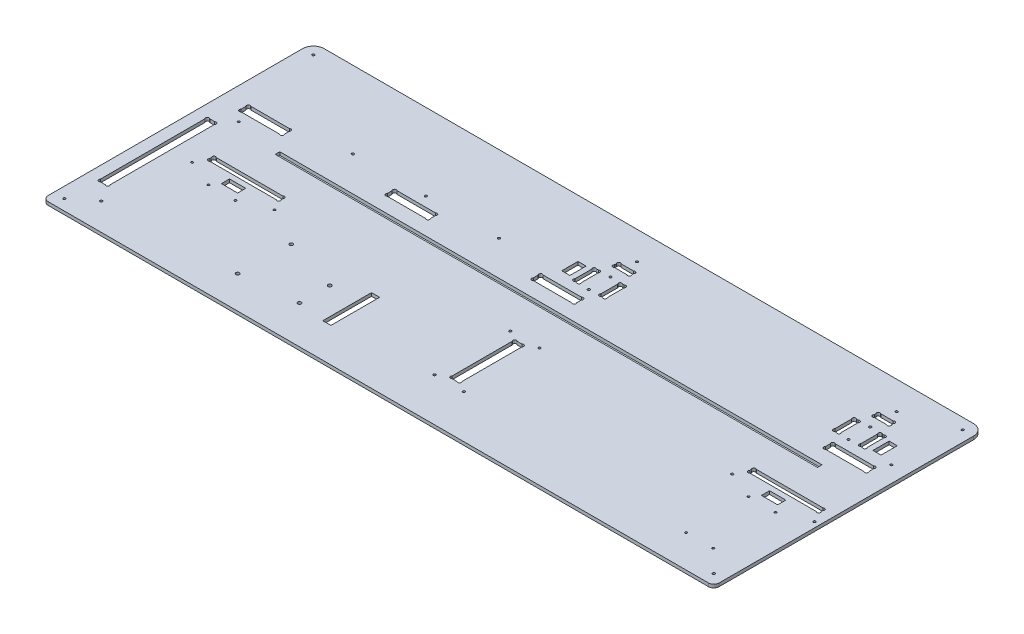
SolidWorks part; units mm, degrees
ref_plane "Plan de face" through (0, 0, 0) normal (0, 0, 1) x (1, 0, 0)
ref_plane "Plan de dessus" through (0, 0, 0) normal (0, 1, 0) x (1, 0, 0)
ref_plane "Plan de droite" through (0, 0, 0) normal (1, 0, 0) x (0, 0, -1)
sketch "Esquisse1" plane through (0, 0, 0) normal (0, 1, 0) x (1, 0, 0)
  line L26 (317, 211.2627) -> (317, 212.7373)
  line L28 (319.2627, 215) -> (330.7373, 215)
  line L29 (333, 211.2627) -> (333, 212.7373)
  line L30 (330.7373, 209) -> (319.2627, 209)
  line L31 (312.2627, 179.5) -> (313.7373, 179.5)
  line L32 (312.2627, 199.5) -> (313.7373, 199.5)
  line L33 (310, 197.2373) -> (310, 181.7627)
  line L34 (316, 181.7627) -> (316, 197.2373)
  line L35 (334, 181.7627) -> (334, 197.2373)
  line L36 (340, 197.2373) -> (340, 181.7627)
  line L37 (337.7373, 199.5) -> (336.2627, 199.5)
  line L38 (337.7373, 179.5) -> (336.2627, 179.5)
  line L39 (552.2627, 179.5) -> (553.7373, 179.5)
  line L40 (552.2627, 199.5) -> (553.7373, 199.5)
  line L41 (550, 197.2373) -> (550, 181.7627)
  line L42 (556, 181.7627) -> (556, 197.2373)
  line L43 (574, 181.7627) -> (574, 197.2373)
  line L44 (580, 197.2373) -> (580, 181.7627)
  line L45 (577.7373, 199.5) -> (576.2627, 199.5)
  line L46 (577.7373, 179.5) -> (576.2627, 179.5)
  line L47 (559.2627, 209) -> (570.7373, 209)
  line L48 (557, 211.2627) -> (557, 212.7373)
  line L49 (570.7373, 215) -> (559.2627, 215)
  line L50 (573, 211.2627) -> (573, 212.7373)
  line L55 (560, 167.7373) -> (560, 163.2627)
  line L56 (600, 167.7373) -> (600, 163.2627)
  line L57 (562.2627, 170) -> (597.7373, 170)
  line L58 (597.7373, 161) -> (562.2627, 161)
  line L59 (292.2627, 161) -> (327.7373, 161)
  line L60 (327.7373, 170) -> (292.2627, 170)
  line L61 (290, 167.7373) -> (290, 163.2627)
  line L62 (330, 167.7373) -> (330, 163.2627)
  line L64 (20, 167.7373) -> (20, 163.2627)
  line L65 (60, 167.7373) -> (60, 163.2627)
  line L66 (22.2627, 170) -> (57.7373, 170)
  line L67 (57.7373, 161) -> (22.2627, 161)
  line L70 (155, 167.7373) -> (155, 163.2627)
  line L71 (195, 167.7373) -> (195, 163.2627)
  line L72 (157.2627, 170) -> (192.7373, 170)
  line L73 (192.7373, 161) -> (157.2627, 161)
  line L76 (10, 250) -> (610, 250)
  line L77 (0, 240) -> (0, 0)
  line L78 (0, 0) -> (620, 0)
  line L79 (620, 240) -> (620, 0)
  line L84 (13.2627, 40) -> (17.7373, 40)
  line L85 (13.2627, 141) -> (17.7373, 141)
  line L86 (11, 138.7373) -> (11, 42.2627)
  line L87 (20, 42.2627) -> (20, 138.7373)
  line L98 (337.7373, 45) -> (333.2627, 45)
  line L99 (337.7373, 105) -> (333.2627, 105)
  line L100 (340, 47.2627) -> (340, 102.7373)
  line L101 (331, 102.7373) -> (331, 47.2627)
  line L109 (610, 109.2627) -> (610, 110.7373)
  line L110 (544, 109.2627) -> (544, 110.7373)
  line L111 (607.7373, 107) -> (546.2627, 107)
  line L112 (546.2627, 113) -> (607.7373, 113)
  line L113 (108.7373, 113) -> (47.2627, 113)
  line L114 (47.2627, 107) -> (108.7373, 107)
  line L115 (111, 109.2627) -> (111, 110.7373)
  line L116 (45, 109.2627) -> (45, 110.7373)
  arc A0 (319.2627, 215) -> (317, 212.7373) centre (318.1314, 213.8686) ccw
  arc A1 (319.2627, 209) -> (317, 211.2627) centre (318.1314, 210.1314) cw
  arc A2 (330.7373, 209) -> (333, 211.2627) centre (331.8686, 210.1314) ccw
  arc A3 (330.7373, 215) -> (333, 212.7373) centre (331.8686, 213.8686) cw
  arc A4 (313.7373, 179.5) -> (316, 181.7627) centre (314.8686, 180.6314) ccw
  arc A5 (312.2627, 179.5) -> (310, 181.7627) centre (311.1314, 180.6314) cw
  arc A6 (312.2627, 199.5) -> (310, 197.2373) centre (311.1314, 198.3686) ccw
  arc A7 (313.7373, 199.5) -> (316, 197.2373) centre (314.8686, 198.3686) cw
  arc A8 (336.2627, 179.5) -> (334, 181.7627) centre (335.1314, 180.6314) cw
  arc A9 (336.2627, 199.5) -> (334, 197.2373) centre (335.1314, 198.3686) ccw
  arc A10 (337.7373, 199.5) -> (340, 197.2373) centre (338.8686, 198.3686) cw
  arc A11 (337.7373, 179.5) -> (340, 181.7627) centre (338.8686, 180.6314) ccw
  arc A12 (552.2627, 179.5) -> (550, 181.7627) centre (551.1314, 180.6314) cw
  arc A13 (552.2627, 199.5) -> (550, 197.2373) centre (551.1314, 198.3686) ccw
  arc A14 (553.7373, 199.5) -> (556, 197.2373) centre (554.8686, 198.3686) cw
  arc A15 (553.7373, 179.5) -> (556, 181.7627) centre (554.8686, 180.6314) ccw
  arc A16 (576.2627, 199.5) -> (574, 197.2373) centre (575.1314, 198.3686) ccw
  arc A17 (577.7373, 199.5) -> (580, 197.2373) centre (578.8686, 198.3686) cw
  arc A18 (577.7373, 179.5) -> (580, 181.7627) centre (578.8686, 180.6314) ccw
  arc A19 (576.2627, 179.5) -> (574, 181.7627) centre (575.1314, 180.6314) cw
  arc A20 (559.2627, 215) -> (557, 212.7373) centre (558.1314, 213.8686) ccw
  arc A21 (559.2627, 209) -> (557, 211.2627) centre (558.1314, 210.1314) cw
  arc A22 (570.7373, 209) -> (573, 211.2627) centre (571.8686, 210.1314) ccw
  arc A23 (570.7373, 215) -> (573, 212.7373) centre (571.8686, 213.8686) cw
  arc A29 (560, 163.2627) -> (562.2627, 161) centre (561.1314, 162.1314) ccw
  arc A30 (560, 167.7373) -> (562.2627, 170) centre (561.1314, 168.8686) cw
  arc A31 (600, 167.7373) -> (597.7373, 170) centre (598.8686, 168.8686) ccw
  arc A32 (600, 163.2627) -> (597.7373, 161) centre (598.8686, 162.1314) cw
  arc A34 (290, 163.2627) -> (292.2627, 161) centre (291.1314, 162.1314) ccw
  arc A35 (290, 167.7373) -> (292.2627, 170) centre (291.1314, 168.8686) cw
  arc A36 (330, 167.7373) -> (327.7373, 170) centre (328.8686, 168.8686) ccw
  arc A37 (330, 163.2627) -> (327.7373, 161) centre (328.8686, 162.1314) cw
  arc A40 (20, 163.2627) -> (22.2627, 161) centre (21.1314, 162.1314) ccw
  arc A41 (20, 167.7373) -> (22.2627, 170) centre (21.1314, 168.8686) cw
  arc A42 (60, 167.7373) -> (57.7373, 170) centre (58.8686, 168.8686) ccw
  arc A43 (60, 163.2627) -> (57.7373, 161) centre (58.8686, 162.1314) cw
  arc A44 (155, 163.2627) -> (157.2627, 161) centre (156.1314, 162.1314) ccw
  arc A45 (155, 167.7373) -> (157.2627, 170) centre (156.1314, 168.8686) cw
  arc A46 (195, 163.2627) -> (192.7373, 161) centre (193.8686, 162.1314) cw
  arc A47 (195, 167.7373) -> (192.7373, 170) centre (193.8686, 168.8686) ccw
  arc A50 (17.7373, 40) -> (20, 42.2627) centre (18.8686, 41.1314) ccw
  arc A52 (13.2627, 40) -> (11, 42.2627) centre (12.1314, 41.1314) cw
  arc A53 (17.7373, 141) -> (20, 138.7373) centre (18.8686, 139.8686) cw
  arc A54 (13.2627, 141) -> (11, 138.7373) centre (12.1314, 139.8686) ccw
  arc A56 (10, 250) -> (0, 240) centre (10, 240) ccw
  arc A57 (610, 250) -> (620, 240) centre (610, 240) cw
  arc A59 (331, 47.2627) -> (333.2627, 45) centre (332.1314, 46.1314) ccw
  arc A60 (340, 47.2627) -> (337.7373, 45) centre (338.8686, 46.1314) cw
  arc A61 (331, 102.7373) -> (333.2627, 105) centre (332.1314, 103.8686) cw
  arc A62 (340, 102.7373) -> (337.7373, 105) centre (338.8686, 103.8686) ccw
  arc A64 (607.7373, 107) -> (610, 109.2627) centre (608.8686, 108.1314) ccw
  circle A65 centre (539, 98) radius 1.1
  arc A66 (607.7373, 113) -> (610, 110.7373) centre (608.8686, 111.8686) cw
  circle A67 centre (615, 98) radius 1.1
  arc A68 (546.2627, 113) -> (544, 110.7373) centre (545.1314, 111.8686) ccw
  arc A69 (546.2627, 107) -> (544, 109.2627) centre (545.1314, 108.1314) cw
  arc A70 (108.7373, 107) -> (111, 109.2627) centre (109.8686, 108.1314) ccw
  arc A71 (108.7373, 113) -> (111, 110.7373) centre (109.8686, 111.8686) cw
  arc A73 (47.2627, 113) -> (45, 110.7373) centre (46.1314, 111.8686) ccw
  arc A75 (47.2627, 107) -> (45, 109.2627) centre (46.1314, 108.1314) cw
  point P1 (337, 199.5)
  point P7 (340, 189.5)
  dimension "D25" = 6
  dimension "D28" = 16
  dimension "D29" = 20
  dimension "D32" = 9.5
  dimension "D33" = 35
  dimension "D39" = 10
  dimension "D49" = 1.1314
  dimension "D57" = 6
  dimension "D55" = 10
  dimension "D62" = 5
  dimension "D63" = 1.6
  dimension "D64" = 9
  dimension "D65" = 1.1314
  dimension "D66" = 1.1314
  dimension "D67" = 620
  dimension "D9" = 2.2627
  dimension "D10" = 1.6
  dimension "D78" = 3.7373
  dimension "D14" = 1.6
  dimension "D36" = 1.6
  dimension "D61" = 1.6
  dimension "D95" = 1.6
  dimension "D107" = 1.6
  dimension "D118" = 1.6
  dimension "D119" = 1.6
  dimension "D128" = 6
  dimension "D141" = 1.6
  dimension "D58" = 2.2
  dimension "D2" = 250
  dimension "D8" = 20
  dimension "D13" = 40
  dimension "D16" = 1.1314
  dimension "D17" = 1.1314
  dimension "D19" = 2.2627
  dimension "D20" = 2.2627
  dimension "D21" = 80
  dimension "D22" = 9
  dimension "D23" = 1.1314
  dimension "D24" = 1.1314
  dimension "D26" = 6
  dimension "D27" = 6
  dimension "D30" = 40
  dimension "D31" = 18
  dimension "D37" = 1.1314
  dimension "D38" = 2.2627
  dimension "D40" = 1.1314
  dimension "D41" = 1.1314
  dimension "D42" = 1.1314
  dimension "D43" = 1.1314
  dimension "D45" = 1
  dimension "D46" = 1.1314
  dimension "D47" = 1.1314
  dimension "D48" = 1.1314
  dimension "D51" = 3.7373
  dimension "D52" = 66
  dimension "D53" = 10
  dimension "D54" = 66
  dimension "D56" = 107
  dimension "D59" = 1.1314
  dimension "D60" = 2.2627
  dimension "D68" = 60
  dimension "D70" = 6
  dimension "D72" = 1.1314
  dimension "D73" = 1.1314
  dimension "D74" = 63.7373
  dimension "D75" = 2.2627
  dimension "D76" = 2.2627
  dimension "D77" = 45
  dimension "D79" = 45
  dimension "D83" = 280
  dimension "D84" = 1.1314
  dimension "D85" = 1.1314
  dimension "D86" = 1.1314
  dimension "D87" = 1.1314
  dimension "D88" = 9
  dimension "D89" = 101
  dimension "D90" = 40
  dimension "D91" = 11
  dimension "D96" = 1.1314
  dimension "D97" = 1.1314
  dimension "D98" = 1.1314
  dimension "D100" = 1.1314
  dimension "D105" = 9
  dimension "D106" = 40
  dimension "D108" = 20
  dimension "D109" = 80
  dimension "D110" = 1.1314
  dimension "D111" = 1.1314
  dimension "D112" = 1.1314
  dimension "D113" = 1.1314
  dimension "D114" = 40
  dimension "D115" = 95
  dimension "D116" = 95
  dimension "D117" = 40
  dimension "D120" = 1.1314
  dimension "D121" = 1.1314
  dimension "D122" = 1.1314
  dimension "D123" = 1.1314
  dimension "D124" = 1.1314
  dimension "D125" = 1.1314
  dimension "D126" = 1.1314
  dimension "D127" = 1.1314
  dimension "D129" = 6
  dimension "D130" = 6
  dimension "D132" = 20
  dimension "D133" = 16
  dimension "D135" = 35
  dimension "D136" = 9.5
  dimension "D139" = 1
  dimension "D140" = 18
  dimension "D142" = 1.1314
  dimension "D143" = 1.1314
  dimension "D144" = 1.1314
  dimension "D145" = 1.1314
  dimension "D146" = 1.1314
  dimension "D147" = 1.1314
  dimension "D148" = 1.1314
  dimension "D149" = 1.1314
  dimension "D150" = 1.1314
  dimension "D151" = 1.1314
  dimension "D152" = 1.1314
  dimension "D153" = 1.1314
  dimension "D154" = 9
  dimension "D155" = 5
extrude "Extrusion1" add sketch "Esquisse1" along normal blind 3
sketch "Esquisse2" plane through (0, 3, 0) normal (0, 1, 0) x (-1, 0, 0)
  line L0 (-610, -250) -> (-10, -250) construction
  line L5 (-620, 21.4973) -> (-620, -261.3021) construction
  line L7 (-573, -142.8) -> (-72, -142.8)
  line L8 (-573, -142.8) -> (-573, -147)
  line L9 (-573, -147) -> (-72, -147)
  line L10 (-72, -142.8) -> (-72, -147)
  dimension "D1" = 47
  dimension "D2" = 4.2
  dimension "D3" = 501
  dimension "D4" = 103
extrude "Enlèv. mat.-Extru.1" cut sketch "Esquisse2" against normal through all
sketch "Esquisse3" plane through (0, 3, 0) normal (0, 1, 0) x (1, 0, 0)
  line L0 (574, 197.2373) -> (574, 181.7627) construction
  line L1 (556, 181.7627) -> (556, 197.2373) construction
  line L2 (559.2627, 209) -> (570.7373, 209) construction
  line L4 (576.2627, 179.5) -> (577.7373, 179.5) construction
  line L5 (577.7373, 199.5) -> (576.2627, 199.5) construction
  line L6 (334, 197.2373) -> (334, 181.7627) construction
  circle A0 centre (565, 179.5) radius 1.1
  circle A1 centre (565, 199.5) radius 1.1
  circle A2 centre (325, 179.5) radius 1.1
  circle A3 centre (325, 199.5) radius 1.1
  dimension "D1" = 2.2
  dimension "D2" = 9
  dimension "D3" = 9
  dimension "D4" = 20
  dimension "D5" = 9.5
  dimension "D6" = 0
  dimension "D7" = 0
  dimension "D8" = 9
extrude "Enlèv. mat.-Extru.2" cut sketch "Esquisse3" against normal through all
fillet "Congé1" radius 5 2 edges at (620, 1.5, 0) (0, 1.5, 0)
sketch "Esquisse4" plane through (0, 0, 0) normal (0, -1, 0) x (1, 0, 0)
  line L0 (0, -240) -> (0, -5) construction
  line L1 (5, 0) -> (615, 0) construction
  line L2 (610, -250) -> (10, -250) construction
  line L3 (620, -5) -> (620, -240) construction
  circle A0 centre (10, -10) radius 1.1
  circle A1 centre (610, -10) radius 1.1
  circle A2 centre (610, -240) radius 1.1
  circle A3 centre (10, -240) radius 1.1
  dimension "D1" = 2.2
  dimension "D2" = 10
  dimension "D3" = 10
  dimension "D4" = 10
  dimension "D5" = 10
  dimension "D6" = 10
  dimension "D7" = 10
  dimension "D8" = 10
  dimension "D9" = 10
extrude "Enlèv. mat.-Extru.3" cut sketch "Esquisse4" against normal through all
sketch "Esquisse5" plane through (0, 3, 0) normal (0, 1, 0) x (1, 0, 0)
  line L1 (0, 240) -> (0, 5) construction
  line L2 (5, 0) -> (615, 0) construction
  circle A0 centre (151.27, 78.26) radius 1.59
  circle A1 centre (150, 30) radius 1.59
  circle A2 centre (202.07, 63.02) radius 1.59
  circle A3 centre (202.07, 35.08) radius 1.59
  dimension "D1" = 3.18
  dimension "D7" = 30
  dimension "D2" = 48.26
  dimension "D3" = 27.94
  dimension "D4" = 52.07
  dimension "D5" = 5.08
  dimension "D6" = 150
  dimension "D8" = 1.27
extrude "Enlèv. mat.-Extru.4" cut sketch "Esquisse5" against normal through all
sketch "Esquisse6" plane through (0, 3, 0) normal (0, 1, 0) x (1, 0, 0)
  line L0 (544, 110.7373) -> (544, 109.2627) construction
  line L1 (569.5, 102) -> (584.5, 102)
  line L2 (569.5, 102) -> (569.5, 94.5)
  line L3 (569.5, 94.5) -> (584.5, 94.5)
  line L4 (584.5, 102) -> (584.5, 94.5)
  line L5 (610, 109.2627) -> (610, 110.7373) construction
  line L6 (546.2627, 107) -> (607.7373, 107) construction
  line L8 (585, 197) -> (592.5, 197)
  line L9 (585, 197) -> (585, 182)
  line L10 (585, 182) -> (592.5, 182)
  line L11 (592.5, 197) -> (592.5, 182)
  line L12 (305, 197) -> (297.5, 197)
  line L13 (305, 197) -> (305, 182)
  line L14 (305, 182) -> (297.5, 182)
  line L15 (297.5, 197) -> (297.5, 182)
  line L16 (577.7373, 199.5) -> (576.2627, 199.5) construction
  line L17 (576.2627, 179.5) -> (577.7373, 179.5) construction
  line L18 (580, 181.7627) -> (580, 197.2373) construction
  line L19 (310, 197.2373) -> (310, 181.7627) construction
  line L20 (313.7373, 199.5) -> (312.2627, 199.5) construction
  line L21 (45, 110.7373) -> (45, 109.2627) construction
  line L22 (227.07, 76.63) -> (234.57, 76.63)
  line L23 (227.07, 76.63) -> (227.07, 31.63)
  line L24 (227.07, 31.63) -> (234.57, 31.63)
  line L25 (234.57, 76.63) -> (234.57, 31.63)
  line L26 (70.5, 102) -> (85.5, 102)
  line L27 (70.5, 102) -> (70.5, 94.5)
  line L28 (70.5, 94.5) -> (85.5, 94.5)
  line L29 (85.5, 102) -> (85.5, 94.5)
  circle A0 centre (150, 30) radius 1.59 construction
  circle A1 centre (151.27, 78.26) radius 1.59 construction
  circle A2 centre (202.07, 63.02) radius 1.59 construction
  dimension "D1" = 15
  dimension "D2" = 7.5
  dimension "D3" = 25.5
  dimension "D4" = 25.5
  dimension "D5" = 5
  dimension "D6" = 7.5
  dimension "D7" = 15
  dimension "D8" = 15
  dimension "D9" = 7.5
  dimension "D10" = 2.5
  dimension "D11" = 2.5
  dimension "D12" = 5
  dimension "D13" = 5
  dimension "D14" = 2.5
  dimension "D15" = 7.5
  dimension "D16" = 45
  dimension "D17" = 1.63
  dimension "D18" = 1.63
  dimension "D19" = 25
  dimension "D20" = 15
  dimension "D21" = 25.5
extrude "Enlèv. mat.-Extru.5" cut sketch "Esquisse6" against normal through all
sketch "Esquisse7" plane through (0, 3, 0) normal (0, 1, 0) x (1, 0, 0)
  line L0 (70.5, 102) -> (70.5, 94.5) construction
  line L1 (85.5, 94.5) -> (85.5, 102) construction
  line L2 (70.5, 94.5) -> (85.5, 94.5) construction
  line L3 (569.5, 94.5) -> (584.5, 94.5) construction
  line L4 (584.5, 94.5) -> (584.5, 102) construction
  line L5 (569.5, 102) -> (569.5, 94.5) construction
  line L6 (47.2627, 107) -> (108.7373, 107) construction
  line L7 (45, 110.7373) -> (45, 109.2627) construction
  line L8 (111, 109.2627) -> (111, 110.7373) construction
  line L9 (5, 0) -> (615, 0) construction
  circle A0 centre (589.5, 87.5) radius 1
  circle A1 centre (564.5, 87.5) radius 1
  circle A6 centre (65.5, 87.5) radius 1
  circle A7 centre (90.5, 87.5) radius 1
  circle A8 centre (116, 98) radius 1
  circle A9 centre (40, 98) radius 1
  circle A10 centre (564.5, 30) radius 1
  circle A11 centre (589.5, 30) radius 1
  point P22 (0, 0)
  point P23 (0, 0)
  point P24 (0, 0)
  point P25 (0, 0)
  point P26 (90.5, 35.8584)
  point P27 (0, 0)
  point P40 (0, 0)
  point P41 (0, 0)
  point P42 (0, 0)
  dimension "D1" = 2
  dimension "D8" = 2
  dimension "D2" = 5
  dimension "D3" = 5
  dimension "D4" = 7
  dimension "D5" = 7
  dimension "D6" = 5
  dimension "D7" = 5
  dimension "D9" = 30
  dimension "D10" = 5
  dimension "D11" = 9
  dimension "D12" = 5
extrude "Enlèv. mat.-Extru.6" cut sketch "Esquisse7" against normal through all
sketch "Esquisse8" plane through (0, 3, 0) normal (0, 1, 0) x (1, 0, 0)
  line L0 (5, 0) -> (615, 0) construction
  line L1 (0, 240) -> (0, 5) construction
  line L2 (330.7373, 215) -> (319.2627, 215) construction
  line L3 (570.7373, 215) -> (559.2627, 215) construction
  line L4 (597.7373, 170) -> (562.2627, 170) construction
  line L5 (331, 102.7373) -> (331, 47.2627) construction
  line L6 (340, 47.2627) -> (340, 102.7373) construction
  line L7 (192.7373, 170) -> (157.2627, 170) construction
  circle A0 centre (29, 25) radius 1.1
  circle A1 centre (29, 152) radius 1.1
  circle A2 centre (107.5, 179) radius 1.1
  circle A3 centre (242.5, 179) radius 1.1
  circle A4 centre (175, 179) radius 1.1
  circle A5 centre (325, 224) radius 1.1
  circle A6 centre (565, 224) radius 1.1
  circle A7 centre (605, 179) radius 1.1
  circle A9 centre (322, 40) radius 1.1
  circle A10 centre (322, 110) radius 1.1
  circle A11 centre (349, 110) radius 1.1
  circle A12 centre (349, 40) radius 1.1
  point P22 (565, 215)
  point P24 (325, 215)
  point P49 (175, 170)
  dimension "D1" = 2.2
  dimension "D4" = 127
  dimension "D5" = 67.5
  dimension "D13" = 9
  dimension "D2" = 25
  dimension "D3" = 29
  dimension "D7" = 9
  dimension "D8" = 67.5
  dimension "D9" = 9
  dimension "D10" = 40
  dimension "D11" = 9
  dimension "D12" = 40
  dimension "D14" = 9
  dimension "D15" = 70
extrude "Enlèv. mat.-Extru.7" cut sketch "Esquisse8" against normal through all
